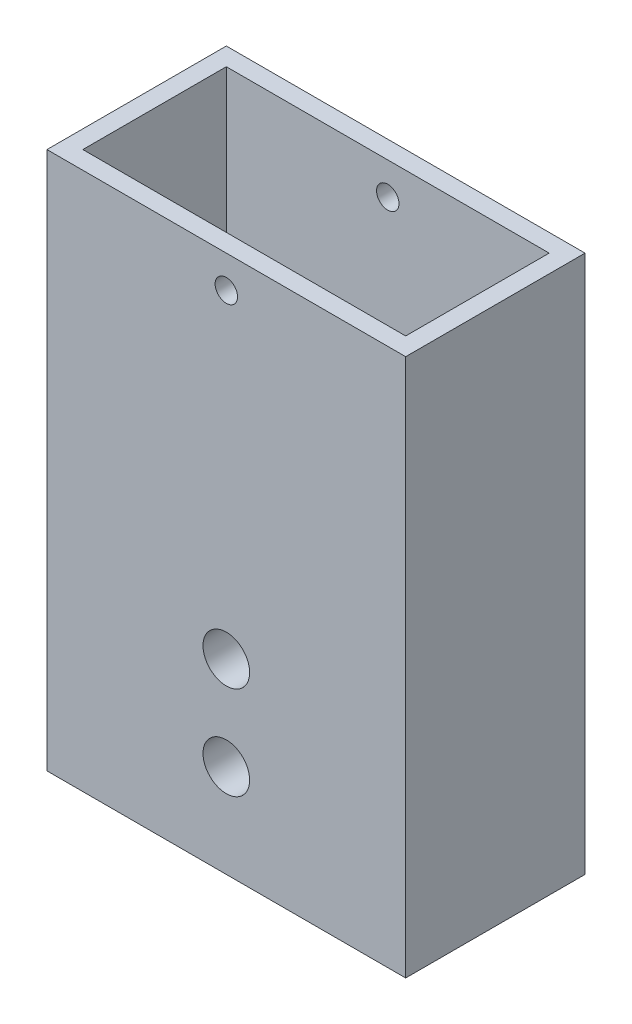
SolidWorks part; units mm, degrees
ref_plane "Front Plane" through (0, 0, 0) normal (0, 0, 1) x (1, 0, 0)
ref_plane "Top Plane" through (0, 0, 0) normal (0, 1, 0) x (1, 0, 0)
ref_plane "Right Plane" through (0, 0, 0) normal (1, 0, 0) x (0, 0, -1)
sketch "Sketch1" plane through (0, 0, 0) normal (0, 0, 1) x (1, 0, 0)
  line L1 (0, 0) -> (50.8, 0)
  line L2 (0, 0) -> (0, 76.2)
  line L3 (0, 76.2) -> (50.8, 76.2)
  line L4 (50.8, 0) -> (50.8, 76.2)
  circle A0 centre (25.4, 13.208) radius 3.302
  circle A1 centre (25.4, 26.416) radius 3.302
  dimension "D3" = 6.604
  dimension "D6" = 6.604
  dimension "D1" = 76.2
  dimension "D2" = 50.8
  dimension "D4" = 13.208
  dimension "D5" = 25.4
  dimension "D7" = 13.208
  dimension "D8" = 25.4
extrude "Boss-Extrude1" add sketch "Sketch1" along normal blind 25.4
sketch "Sketch2" plane through (0, 76.2, 0) normal (0, 1, 0) x (1, 0, 0)
  line L0 (0, -25.4) -> (0, 0) construction
  line L1 (2.54, -2.54) -> (48.26, -2.54)
  line L2 (2.54, -2.54) -> (2.54, -22.86)
  line L3 (2.54, -22.86) -> (48.26, -22.86)
  line L4 (48.26, -2.54) -> (48.26, -22.86)
  line L5 (50.8, -25.4) -> (50.8, 0) construction
  line L6 (50.8, -25.4) -> (0, -25.4) construction
  line L7 (50.8, 0) -> (0, 0) construction
  dimension "D1" = 2.54
  dimension "D2" = 2.54
  dimension "D3" = 2.54
  dimension "D4" = 2.54
extrude "Cut-Extrude1" cut sketch "Sketch2" against normal blind 38.1
sketch "Sketch3" plane through (0, 0, 25.4) normal (0, 0, 1) x (1, 0, 0)
  line L0 (50.8, 76.2) -> (0, 76.2) construction
  circle A0 centre (25.4, 71.628) radius 1.5875
  dimension "D1" = 3.175
  dimension "D2" = 4.572
extrude "Cut-Extrude2" cut sketch "Sketch3" against normal through all
